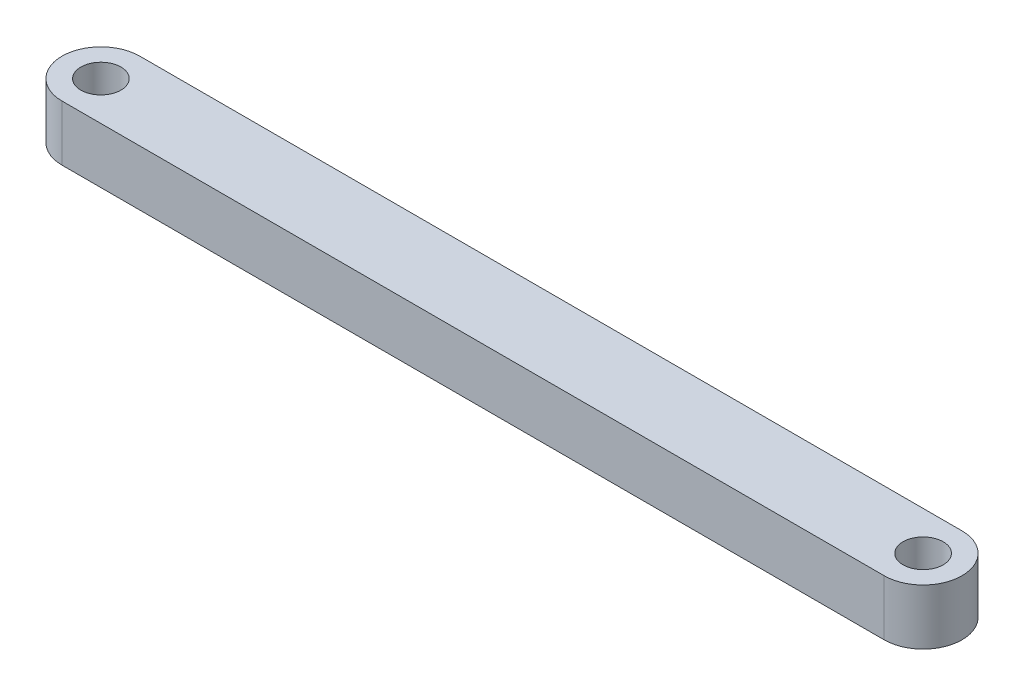
SolidWorks part; units mm, degrees
ref_plane "Front Plane" through (0, 0, 0) normal (0, 0, 1) x (1, 0, 0)
ref_plane "Top Plane" through (0, 0, 0) normal (0, 1, 0) x (1, 0, 0)
ref_plane "Right Plane" through (0, 0, 0) normal (1, 0, 0) x (0, 0, -1)
sketch "Sketch1" plane through (0, 0, 0) normal (0, 1, 0) x (1, 0, 0)
  line L0 (4.445, 8.89) -> (98.425, 8.89)
  line L2 (98.425, 0) -> (4.445, 0)
  arc A0 (4.445, 0) -> (4.445, 8.89) centre (4.445, 4.445) cw
  arc A1 (98.425, 8.89) -> (98.425, 0) centre (98.425, 4.445) cw
  circle A2 centre (4.445, 4.445) radius 2.2924
  circle A3 centre (98.425, 4.445) radius 2.2923
  point P7 (0, 4.445)
  dimension "D3" = 4.5847
  dimension "D4" = 4.5847
  dimension "D1" = 8.89
  dimension "D2" = 93.98
extrude "Boss-Extrude1" add sketch "Sketch1" along normal blind 6.35
